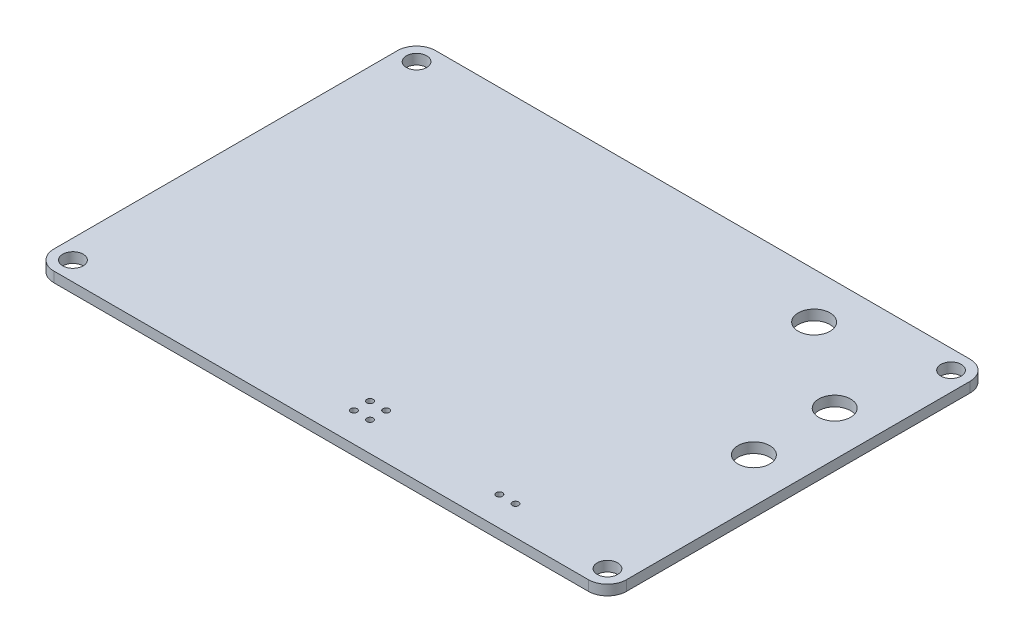
SolidWorks part; units mm, degrees
ref_plane "Front" through (0, 0, 0) normal (0, 0, 1) x (1, 0, 0)
ref_plane "Top" through (0, 0, 0) normal (0, 1, 0) x (1, 0, 0)
ref_plane "Right" through (0, 0, 0) normal (1, 0, 0) x (0, 0, -1)
sketch "Sketch1" plane through (0, 0, 0) normal (0, 1, 0) x (1, 0, 0)
  line L1 (45, -30) -> (-45, -30)
  line L2 (45, -30) -> (45, 30)
  line L3 (45, 30) -> (-45, 30)
  line L4 (-45, -30) -> (-45, 30)
  line L5 (45, -30) -> (-45, 30) construction
  line L6 (45, 30) -> (-45, -30) construction
  point P0 (0, 0)
  dimension "D1" = 90
  dimension "D2" = 60
extrude "Boss-Extrude1" add sketch "Sketch1" along normal blind 1.6
sketch "Sketch2" plane through (0, 1.6, 0) normal (0, 1, 0) x (-1, 0, 0)
  line L0 (-45, -30) -> (45, -30) construction
  line L1 (45, -30) -> (45, 30) construction
  line L2 (-45, 30) -> (-45, -30) construction
  line L3 (45, 30) -> (-45, 30) construction
  circle A0 centre (42, -27) radius 1.6
  circle A1 centre (42, 27) radius 1.6
  circle A2 centre (-42, 27) radius 1.6
  circle A3 centre (-42, -27) radius 1.6
  dimension "D1" = 3.2
  dimension "D3" = 3
  dimension "D2" = 3
  dimension "D4" = 3
  dimension "D5" = 3
extrude "Cut-Extrude1" cut sketch "Sketch2" against normal blind 1.6
fillet "Fillet1" radius 3 4 edges at (45, 0.8, -30) (45, 0.8, 30) (-45, 0.8, 30) (-45, 0.8, -30)
sketch "Sketch3" plane through (0, 1.6, 0) normal (0, 1, 0) x (-1, 0, 0)
  line L0 (45, 0) -> (-45, 0) construction
  line L1 (45, -27) -> (45, 27) construction
  line L2 (-45, 27) -> (-45, -27) construction
  line L3 (-42, -30) -> (42, -30) construction
  circle A0 centre (-0.55, 25.4) radius 0.5
  circle A1 centre (-0.55, 22.86) radius 0.5
  circle A2 centre (-3.09, 25.4) radius 0.5
  circle A3 centre (-3.09, 22.86) radius 0.5
  circle A4 centre (-23.41, 25.4) radius 0.5
  circle A5 centre (-25.95, 25.4) radius 0.5
  circle A6 centre (-38.015, 0) radius 2.5
  circle A7 centre (-38.015, -12.7) radius 2.5
  circle A8 centre (-24.68, -22.8) radius 2.5
  dimension "D1" = 1
  dimension "D2" = 1
  dimension "D3" = 1
  dimension "D4" = 1
  dimension "D5" = 1
  dimension "D6" = 1
  dimension "D7" = 5
  dimension "D8" = 5
  dimension "D9" = 5
  dimension "D10" = 25.4
  dimension "D11" = 44.45
  dimension "D12" = 21.59
  dimension "D13" = 41.91
  dimension "D14" = 22.86
  dimension "D15" = 19.05
  dimension "D16" = 6.985
  dimension "D17" = 12.7
  dimension "D18" = 20.32
  dimension "D19" = 7.2
extrude "Cut-Extrude2" cut sketch "Sketch3" against normal blind 1.6
